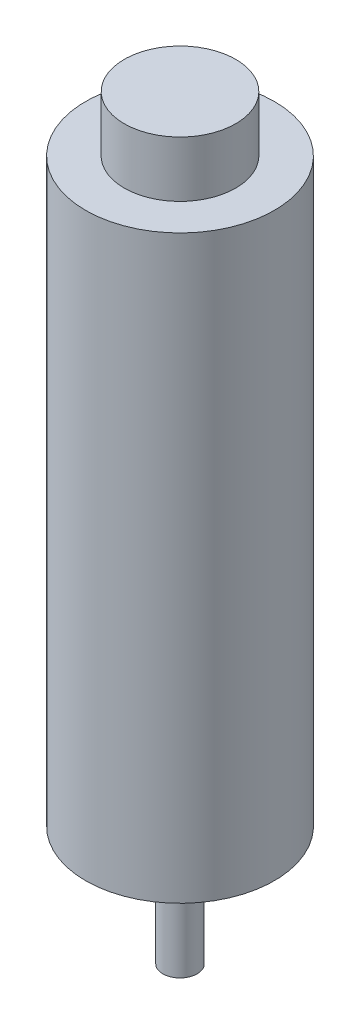
SolidWorks part; units mm, degrees
material "Plain Carbon Steel"
ref_plane "Front Plane" through (0, 0, 0) normal (0, 0, 1) x (1, 0, 0)
ref_plane "Top Plane" through (0, 0, 0) normal (0, 1, 0) x (1, 0, 0)
ref_plane "Right Plane" through (0, 0, 0) normal (1, 0, 0) x (0, 0, -1)
sketch "Sketch1" plane through (0, 0, 0) normal (0, 1, 0) x (1, 0, 0)
  circle A0 centre (0, 0) radius 11
  dimension "D1" = 22
extrude "Boss-Extrude1" add sketch "Sketch1" along normal mid plane 67.67
sketch "Sketch2" plane through (0, 33.835, 0) normal (0, 1, 0) x (1, 0, 0)
  circle A0 centre (0, 0) radius 6.5
  dimension "D1" = 13
extrude "Boss-Extrude2" add sketch "Sketch2" along normal blind 6.5
sketch "Sketch3" plane through (0, -33.835, 0) normal (0, -1, 0) x (1, 0, 0)
  circle A0 centre (0, 0) radius 5
  dimension "D1" = 10
extrude "Boss-Extrude3" add sketch "Sketch3" along normal blind 1
sketch "Sketch4" plane through (0, -34.835, 0) normal (0, -1, 0) x (-1, 0, 0)
  circle A0 centre (0, 0) radius 3.5
  dimension "D1" = 7
extrude "Boss-Extrude4" add sketch "Sketch4" along normal blind 2
sketch "Sketch5" plane through (0, -36.835, 0) normal (0, -1, 0) x (1, 0, 0)
  circle A0 centre (0, 0) radius 2
  dimension "D1" = 4
extrude "Boss-Extrude5" add sketch "Sketch5" along normal blind 10.9
